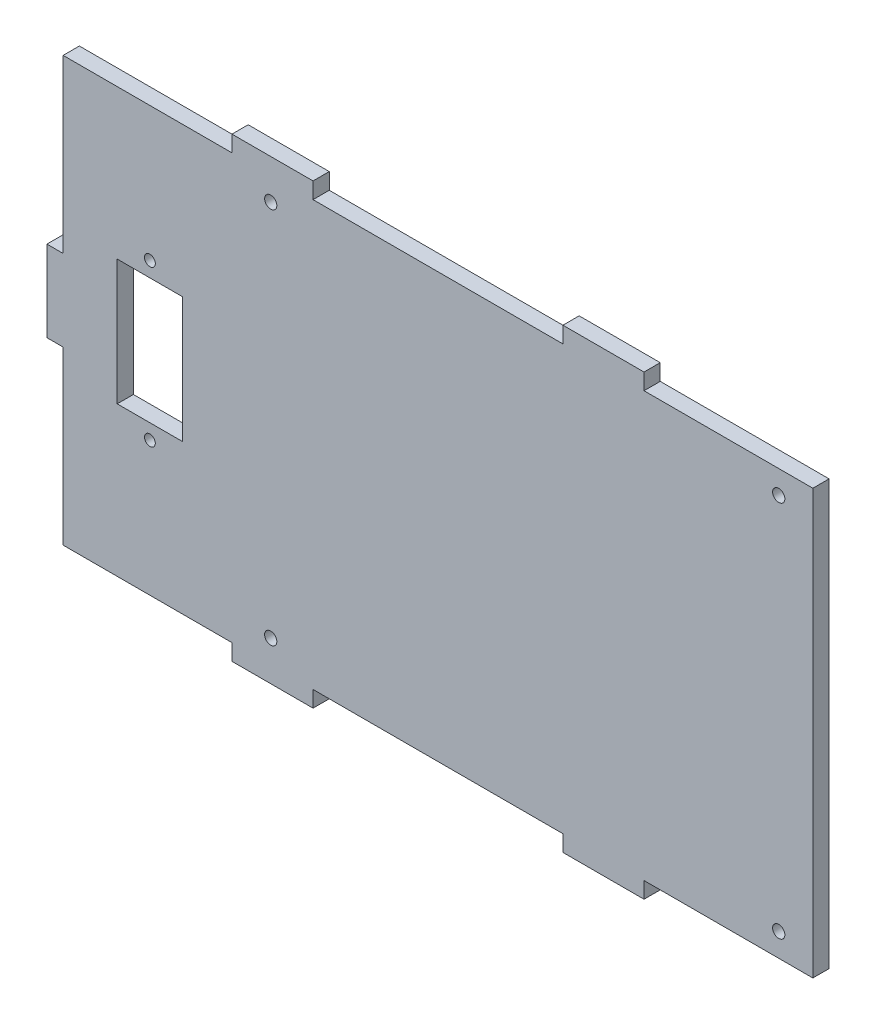
SolidWorks part; units mm, degrees
ref_plane "Front Plane" through (0, 0, 0) normal (0, 0, 1) x (1, 0, 0)
ref_plane "Top Plane" through (0, 0, 0) normal (0, 1, 0) x (1, 0, 0)
ref_plane "Right Plane" through (0, 0, 0) normal (1, 0, 0) x (0, 0, -1)
sketch "Sketch1" plane through (0, 0, 0) normal (0, 0, 1) x (1, 0, 0)
  line L0 (-36.5479, 71.49) -> (-5.3179, 71.49)
  line L1 (-5.3179, 71.49) -> (-5.3179, 74.49)
  line L2 (-36.5479, -6.98) -> (-36.5479, 24.755)
  line L3 (-36.5479, -6.98) -> (-5.3179, -6.98)
  line L4 (102.1451, 71.49) -> (102.1421, -6.98)
  line L5 (-5.3179, 74.49) -> (9.6821, 74.49)
  line L6 (9.6821, 74.49) -> (9.6821, 71.49)
  line L7 (9.6821, 71.49) -> (55.9121, 71.49)
  line L8 (55.9121, 71.49) -> (55.9121, 74.49)
  line L9 (55.9121, 74.49) -> (70.9121, 74.49)
  line L10 (70.9121, 74.49) -> (70.9121, 71.49)
  line L11 (70.9121, 71.49) -> (102.1451, 71.49)
  line L12 (-5.3179, -6.98) -> (-5.3179, -9.98)
  line L13 (-5.3179, -9.98) -> (9.6821, -9.98)
  line L14 (9.6821, -9.98) -> (9.6821, -6.98)
  line L15 (9.6821, -6.98) -> (55.9121, -6.98)
  line L16 (55.9121, -6.98) -> (55.9121, -9.98)
  line L17 (55.9121, -9.98) -> (70.9121, -9.98)
  line L18 (70.9121, -9.98) -> (70.9121, -6.98)
  line L19 (70.9121, -6.98) -> (102.1421, -6.98)
  line L20 (-36.5479, 24.755) -> (-39.5479, 24.755)
  line L21 (-39.5479, 24.755) -> (-39.5479, 39.755)
  line L22 (-39.5479, 39.755) -> (-36.5479, 39.755)
  line L23 (-36.5479, 39.755) -> (-36.5479, 71.49)
  dimension "D1" = 15
  dimension "D3" = 15
  dimension "D4" = 15
  dimension "D5" = 15
  dimension "D6" = 31.23
  dimension "D7" = 46.23
  dimension "D8" = 31.233
  dimension "D9" = 31.23
  dimension "D10" = 31.23
  dimension "D11" = 3
  dimension "D12" = 3
  dimension "D13" = 3
  dimension "D14" = 3
  dimension "D15" = 31.735
  dimension "D16" = 3
  dimension "D17" = 15
  dimension "D18" = 78.47
  dimension "D19" = 3
  dimension "D20" = 31.735
extrude "Boss-Extrude1" add sketch "Sketch1" along normal blind 3
sketch "Sketch2" plane through (0, 0, 3) normal (0, 0, 1) x (1, 0, 0)
  line L0 (102.1451, 71.49) -> (70.9121, 71.49) construction
  line L1 (55.9121, 71.49) -> (9.6821, 71.49) construction
  line L2 (70.9121, -6.98) -> (102.1421, -6.98) construction
  line L3 (9.6821, -6.98) -> (55.9121, -6.98) construction
  line L4 (102.1421, -6.98) -> (102.1451, 71.49) construction
  circle A0 centre (95.8349, 67.18) radius 1.13
  circle A1 centre (95.8322, -2.67) radius 1.13
  circle A2 centre (1.8549, 67.18) radius 1.13
  circle A3 centre (1.8522, -2.67) radius 1.13
  dimension "D1" = 2.26
  dimension "D2" = 2.26
  dimension "D3" = 2.26
  dimension "D4" = 2.26
  dimension "D5" = 4.31
  dimension "D6" = 4.31
  dimension "D7" = 4.31
  dimension "D8" = 4.31
  dimension "D9" = 100.29
  dimension "D10" = 6.31
  dimension "D11" = 100.29
  dimension "D12" = 6.31
extrude "Cut-Extrude1" cut sketch "Sketch2" against normal blind 3
sketch "Sketch3" plane through (0, 0, 3) normal (0, 0, 1) x (1, 0, 0)
  line L0 (-36.5479, 24.755) -> (-36.5479, -6.98) construction
  line L1 (-26.5479, 43.86) -> (-14.4479, 43.86)
  line L2 (-26.5479, 43.86) -> (-26.5479, 20.66)
  line L3 (-26.5479, 20.66) -> (-14.4479, 20.66)
  line L4 (-14.4479, 43.86) -> (-14.4479, 20.66)
  line L5 (-5.3179, 71.49) -> (-36.5479, 71.49) construction
  circle A0 centre (-20.4979, 46.66) radius 1
  circle A1 centre (-20.4979, 17.86) radius 1
  point P12 (-20.4979, 43.86)
  point P13 (-20.4979, 20.66)
  dimension "D5" = 2
  dimension "D6" = 2
  dimension "D1" = 23.2
  dimension "D2" = 12.1
  dimension "D3" = 10
  dimension "D4" = 27.63
  dimension "D7" = 2.8
  dimension "D8" = 2.8
extrude "Cut-Extrude4" cut sketch "Sketch3" against normal blind 3
equation "\"t\"=3"
equation "\"ws\"=15"
equation "\"wb\"=15"
equation "\"D1@Sketch1\"=\"wb\""
equation "\"D3@Sketch1\"=\"wb\""
equation "\"D4@Sketch1\"=\"wb\""
equation "\"D5@Sketch1\"=\"wb\""
equation "\"D6@Sketch1\"=46.23- \"wb\""
equation "\"D8@Sketch1\"=46.233-\"wb\""
equation "\"D9@Sketch1\"=46.23-\"wb\""
equation "\"D10@Sketch1\"=46.23-\"wb\""
equation "\"D11@Sketch1\"=\"t\""
equation "\"D12@Sketch1\"=\"t\""
equation "\"D13@Sketch1\"=\"t\""
equation "\"D14@Sketch1\"=\"t\""
equation "\"D16@Sketch1\"=\"t\""
equation "\"D17@Sketch1\"=\"wb\""
equation "\"D19@Sketch1\"=\"t\""
equation "\"boardhole\"=2.26"
equation "\"D4@Sketch2\"=\"boardhole\""
equation "\"D1@Sketch2\"=\"boardhole\""
equation "\"D2@Sketch2\"=\"boardhole\""
equation "\"D3@Sketch2\"=\"boardhole\""
equation "\"flangehole\"=2"
equation "\"D5@Sketch3\"=\"flangehole\""
equation "\"D6@Sketch3\"=\"flangehole\""
